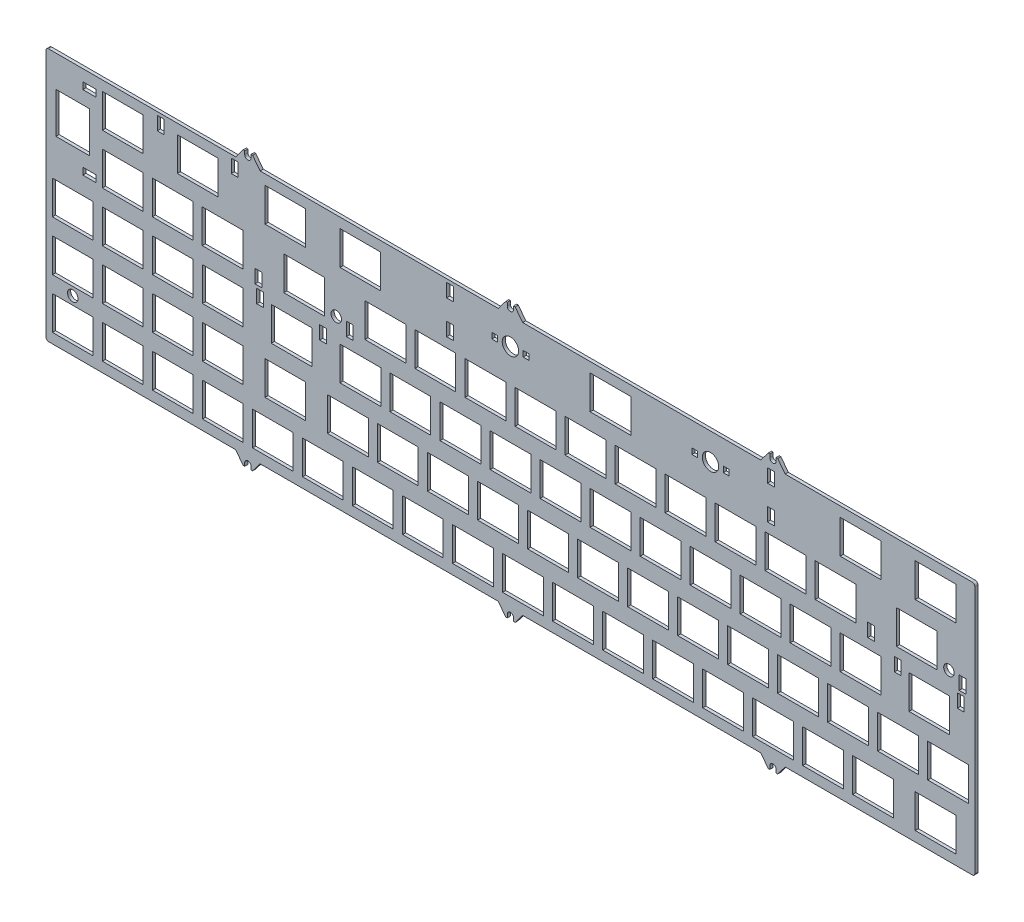
SolidWorks part; units mm, degrees
ref_plane "Front Plane" through (0, 0, 0) normal (0, 0, 1) x (1, 0, 0)
ref_plane "Top Plane" through (0, 0, 0) normal (0, 1, 0) x (1, 0, 0)
ref_plane "Right Plane" through (0, 0, 0) normal (1, 0, 0) x (0, 0, -1)
sketch "Sketch2" plane through (0, 0, 0) normal (0, 0, -1) x (1, 0, 0)
  line L0 (137.0625, 39.4) -> (121.4625, 39.4)
  line L1 (121.4625, 39.4) -> (121.4625, 26.6)
  line L2 (121.4625, 26.6) -> (137.0625, 26.6)
  line L3 (137.0625, 26.6) -> (137.0625, 39.4)
  line L4 (127.5375, 58.45) -> (111.9375, 58.45)
  line L5 (111.9375, 58.45) -> (111.9375, 45.65)
  line L6 (111.9375, 45.65) -> (127.5375, 45.65)
  line L7 (127.5375, 45.65) -> (127.5375, 58.45)
  line L8 (122.775, 77.5) -> (107.175, 77.5)
  line L9 (107.175, 77.5) -> (107.175, 64.7)
  line L10 (107.175, 64.7) -> (122.775, 64.7)
  line L11 (122.775, 64.7) -> (122.775, 77.5)
  line L12 (325.7312, 43.1) -> (325.7312, 48.2)
  line L13 (325.7312, 48.2) -> (323.1312, 48.2)
  line L14 (323.1312, 48.2) -> (323.1312, 43.1)
  line L15 (323.1312, 43.1) -> (325.7312, 43.1)
  line L16 (347.1312, 43.1) -> (347.1312, 48.2)
  line L17 (347.1312, 48.2) -> (349.7312, 48.2)
  line L18 (349.7312, 48.2) -> (349.7312, 43.1)
  line L19 (349.7312, 43.1) -> (347.1312, 43.1)
  line L20 (104.2437, 43.1) -> (104.2437, 48.2)
  line L21 (104.2437, 48.2) -> (106.8437, 48.2)
  line L22 (106.8437, 48.2) -> (106.8437, 43.1)
  line L23 (106.8437, 43.1) -> (104.2437, 43.1)
  line L24 (315.5687, 36.85) -> (315.5687, 41.95)
  line L25 (315.5687, 41.95) -> (312.9687, 41.95)
  line L26 (312.9687, 41.95) -> (312.9687, 36.85)
  line L27 (312.9687, 36.85) -> (315.5687, 36.85)
  line L28 (347.7687, 36.85) -> (347.7687, 41.95)
  line L29 (347.7687, 41.95) -> (350.3687, 41.95)
  line L30 (350.3687, 41.95) -> (350.3687, 36.85)
  line L31 (350.3687, 36.85) -> (347.7687, 36.85)
  line L32 (114.4062, 36.85) -> (114.4062, 41.95)
  line L33 (114.4062, 41.95) -> (117.0062, 41.95)
  line L34 (117.0062, 41.95) -> (117.0062, 36.85)
  line L35 (117.0062, 36.85) -> (114.4062, 36.85)
  line L36 (155.1875, 5) -> (155.1875, 10.1)
  line L37 (155.1875, 10.1) -> (152.5875, 10.1)
  line L38 (152.5875, 10.1) -> (152.5875, 5)
  line L39 (152.5875, 5) -> (155.1875, 5)
  line L40 (183.9625, 15.05) -> (183.9625, 12.85)
  line L41 (183.9625, 12.85) -> (181.7625, 12.85)
  line L42 (181.7625, 12.85) -> (181.7625, 15.05)
  line L43 (181.7625, 15.05) -> (183.9625, 15.05)
  line L44 (169.8125, 12.85) -> (169.8125, 15.05)
  line L45 (169.8125, 15.05) -> (172.0125, 15.05)
  line L46 (172.0125, 15.05) -> (172.0125, 12.85)
  line L47 (172.0125, 12.85) -> (169.8125, 12.85)
  line L48 (246.0125, 15.05) -> (246.0125, 12.85)
  line L49 (246.0125, 12.85) -> (248.2125, 12.85)
  line L50 (248.2125, 12.85) -> (248.2125, 15.05)
  line L51 (248.2125, 15.05) -> (246.0125, 15.05)
  line L52 (260.1625, 12.85) -> (260.1625, 15.05)
  line L53 (260.1625, 15.05) -> (257.9625, 15.05)
  line L54 (257.9625, 15.05) -> (257.9625, 12.85)
  line L55 (257.9625, 12.85) -> (260.1625, 12.85)
  line L56 (82.8437, 43.1) -> (82.8437, 48.2)
  line L57 (82.8437, 48.2) -> (80.2437, 48.2)
  line L58 (80.2437, 48.2) -> (80.2437, 43.1)
  line L59 (80.2437, 43.1) -> (82.8437, 43.1)
  line L60 (82.2062, 36.85) -> (82.2062, 41.95)
  line L61 (82.2062, 41.95) -> (79.6062, 41.95)
  line L62 (79.6062, 41.95) -> (79.6062, 36.85)
  line L63 (79.6062, 36.85) -> (82.2062, 36.85)
  line L64 (44.975, 5) -> (44.975, 10.1)
  line L65 (44.975, 10.1) -> (42.375, 10.1)
  line L66 (42.375, 10.1) -> (42.375, 5)
  line L67 (42.375, 5) -> (44.975, 5)
  line L68 (70.575, 5) -> (70.575, 10.1)
  line L69 (70.575, 10.1) -> (73.175, 10.1)
  line L70 (73.175, 10.1) -> (73.175, 5)
  line L71 (73.175, 5) -> (70.575, 5)
  line L72 (19.125, 10.675) -> (14.025, 10.675)
  line L73 (14.025, 10.675) -> (14.025, 8.075)
  line L74 (14.025, 8.075) -> (19.125, 8.075)
  line L75 (19.125, 8.075) -> (19.125, 10.675)
  line L76 (19.125, 36.275) -> (14.025, 36.275)
  line L77 (14.025, 36.275) -> (14.025, 38.875)
  line L78 (14.025, 38.875) -> (19.125, 38.875)
  line L79 (19.125, 38.875) -> (19.125, 36.275)
  line L80 (155.1875, 22.9) -> (155.1875, 17.8)
  line L81 (155.1875, 17.8) -> (152.5875, 17.8)
  line L82 (152.5875, 17.8) -> (152.5875, 22.9)
  line L83 (152.5875, 22.9) -> (155.1875, 22.9)
  line L84 (277.3875, 22.9) -> (277.3875, 17.8)
  line L85 (277.3875, 17.8) -> (274.7875, 17.8)
  line L86 (274.7875, 17.8) -> (274.7875, 22.9)
  line L87 (274.7875, 22.9) -> (277.3875, 22.9)
  line L88 (274.7875, 5) -> (274.7875, 10.1)
  line L89 (274.7875, 10.1) -> (277.3875, 10.1)
  line L90 (277.3875, 10.1) -> (277.3875, 5)
  line L91 (277.3875, 5) -> (274.7875, 5)
  line L92 (0, 4.75) -> (0, 99.35)
  line L93 (353.775, 4.75) -> (353.775, 99.35)
  line L94 (75.0875, 104.1) -> (72.2375, 100.35)
  line L95 (75.0875, 104.1) -> (75.6875, 104.1)
  line L96 (75.6875, 104.1) -> (75.6875, 103.6)
  line L97 (78.6875, 104.1) -> (81.5375, 100.35)
  line L98 (78.6875, 104.1) -> (78.0875, 104.1)
  line L99 (78.0875, 104.1) -> (78.0875, 103.6)
  line L100 (175.0875, 104.1) -> (172.2375, 100.35)
  line L101 (175.0875, 104.1) -> (175.6875, 104.1)
  line L102 (178.6875, 104.1) -> (181.5375, 100.35)
  line L103 (178.6875, 104.1) -> (178.0875, 104.1)
  line L104 (275.0875, 104.1) -> (272.2375, 100.35)
  line L105 (275.0875, 104.1) -> (275.6875, 104.1)
  line L106 (278.6875, 104.1) -> (281.5375, 100.35)
  line L107 (278.6875, 104.1) -> (278.0875, 104.1)
  line L108 (272.2375, 100.35) -> (181.5375, 100.35)
  line L109 (172.2375, 100.35) -> (81.5375, 100.35)
  line L110 (72.2375, 100.35) -> (1, 100.35)
  line L111 (352.775, 100.35) -> (281.5375, 100.35)
  line L112 (272.2375, 3.75) -> (181.5375, 3.75)
  line L113 (172.2375, 3.75) -> (81.5375, 3.75)
  line L114 (72.2375, 3.75) -> (1, 3.75)
  line L115 (352.775, 3.75) -> (281.5375, 3.75)
  line L116 (331.0625, 83.75) -> (346.5625, 83.75)
  line L117 (346.5625, 83.75) -> (346.5625, 96.55)
  line L118 (346.5625, 96.55) -> (331.0625, 96.55)
  line L119 (331.0625, 96.55) -> (331.0625, 83.75)
  line L120 (307.25, 83.75) -> (322.75, 83.75)
  line L121 (322.75, 83.75) -> (322.75, 96.55)
  line L122 (322.75, 96.55) -> (307.25, 96.55)
  line L123 (307.25, 96.55) -> (307.25, 83.75)
  line L124 (288.2, 83.75) -> (303.7, 83.75)
  line L125 (303.7, 83.75) -> (303.7, 96.55)
  line L126 (303.7, 96.55) -> (288.2, 96.55)
  line L127 (288.2, 96.55) -> (288.2, 83.75)
  line L128 (269.15, 83.75) -> (284.65, 83.75)
  line L129 (284.65, 83.75) -> (284.65, 96.55)
  line L130 (284.65, 96.55) -> (269.15, 96.55)
  line L131 (269.15, 96.55) -> (269.15, 83.75)
  line L132 (250.1, 83.75) -> (265.6, 83.75)
  line L133 (265.6, 83.75) -> (265.6, 96.55)
  line L134 (265.6, 96.55) -> (250.1, 96.55)
  line L135 (250.1, 96.55) -> (250.1, 83.75)
  line L136 (231.05, 83.75) -> (246.55, 83.75)
  line L137 (246.55, 83.75) -> (246.55, 96.55)
  line L138 (246.55, 96.55) -> (231.05, 96.55)
  line L139 (231.05, 96.55) -> (231.05, 83.75)
  line L140 (212, 83.75) -> (227.5, 83.75)
  line L141 (227.5, 83.75) -> (227.5, 96.55)
  line L142 (227.5, 96.55) -> (212, 96.55)
  line L143 (212, 96.55) -> (212, 83.75)
  line L144 (192.95, 83.75) -> (208.45, 83.75)
  line L145 (208.45, 83.75) -> (208.45, 96.55)
  line L146 (208.45, 96.55) -> (192.95, 96.55)
  line L147 (192.95, 96.55) -> (192.95, 83.75)
  line L148 (173.9, 83.75) -> (189.4, 83.75)
  line L149 (189.4, 83.75) -> (189.4, 96.55)
  line L150 (189.4, 96.55) -> (173.9, 96.55)
  line L151 (173.9, 96.55) -> (173.9, 83.75)
  line L152 (154.85, 83.75) -> (170.35, 83.75)
  line L153 (170.35, 83.75) -> (170.35, 96.55)
  line L154 (170.35, 96.55) -> (154.85, 96.55)
  line L155 (154.85, 96.55) -> (154.85, 83.75)
  line L156 (135.8, 83.75) -> (151.3, 83.75)
  line L157 (151.3, 83.75) -> (151.3, 96.55)
  line L158 (151.3, 96.55) -> (135.8, 96.55)
  line L159 (135.8, 96.55) -> (135.8, 83.75)
  line L160 (116.75, 83.75) -> (132.25, 83.75)
  line L161 (132.25, 83.75) -> (132.25, 96.55)
  line L162 (132.25, 96.55) -> (116.75, 96.55)
  line L163 (116.75, 96.55) -> (116.75, 83.75)
  line L164 (97.7, 83.75) -> (113.2, 83.75)
  line L165 (113.2, 83.75) -> (113.2, 96.55)
  line L166 (113.2, 96.55) -> (97.7, 96.55)
  line L167 (97.7, 96.55) -> (97.7, 83.75)
  line L168 (78.65, 83.75) -> (94.15, 83.75)
  line L169 (94.15, 83.75) -> (94.15, 96.55)
  line L170 (94.15, 96.55) -> (78.65, 96.55)
  line L171 (78.65, 96.55) -> (78.65, 83.75)
  line L172 (59.6, 77.5) -> (75.1, 77.5)
  line L173 (75.1, 64.7) -> (75.1, 77.5)
  line L174 (75.1, 96.55) -> (59.6, 96.55)
  line L175 (59.6, 77.5) -> (59.6, 64.7)
  line L176 (40.55, 77.5) -> (56.05, 77.5)
  line L177 (56.05, 64.7) -> (56.05, 77.5)
  line L178 (56.05, 96.55) -> (40.55, 96.55)
  line L179 (40.55, 77.5) -> (40.55, 64.7)
  line L180 (21.5, 77.5) -> (37, 77.5)
  line L181 (37, 64.7) -> (37, 77.5)
  line L182 (37, 96.55) -> (21.5, 96.55)
  line L183 (21.5, 77.5) -> (21.5, 64.7)
  line L184 (2.45, 77.5) -> (17.95, 77.5)
  line L185 (17.95, 64.7) -> (17.95, 77.5)
  line L186 (17.95, 96.55) -> (2.45, 96.55)
  line L187 (2.45, 77.5) -> (2.45, 64.7)
  line L188 (59.6, 64.7) -> (75.1, 64.7)
  line L189 (75.1, 83.75) -> (75.1, 96.55)
  line L190 (75.1, 83.75) -> (59.6, 83.75)
  line L191 (59.6, 96.55) -> (59.6, 83.75)
  line L192 (40.55, 64.7) -> (56.05, 64.7)
  line L193 (56.05, 83.75) -> (56.05, 96.55)
  line L194 (56.05, 83.75) -> (40.55, 83.75)
  line L195 (40.55, 96.55) -> (40.55, 83.75)
  line L196 (21.5, 64.7) -> (37, 64.7)
  line L197 (37, 83.75) -> (37, 96.55)
  line L198 (37, 83.75) -> (21.5, 83.75)
  line L199 (21.5, 96.55) -> (21.5, 83.75)
  line L200 (2.45, 64.7) -> (17.95, 64.7)
  line L201 (17.95, 83.75) -> (17.95, 96.55)
  line L202 (17.95, 83.75) -> (2.45, 83.75)
  line L203 (2.45, 96.55) -> (2.45, 83.75)
  line L204 (59.55, 45.65) -> (75.05, 45.65)
  line L205 (75.05, 45.65) -> (75.05, 58.45)
  line L206 (75.05, 58.45) -> (59.55, 58.45)
  line L207 (59.55, 58.45) -> (59.55, 45.65)
  line L208 (40.5, 45.65) -> (56, 45.65)
  line L209 (56, 45.65) -> (56, 58.45)
  line L210 (56, 58.45) -> (40.5, 58.45)
  line L211 (40.5, 58.45) -> (40.5, 45.65)
  line L212 (21.45, 45.65) -> (36.95, 45.65)
  line L213 (36.95, 45.65) -> (36.95, 58.45)
  line L214 (36.95, 58.45) -> (21.45, 58.45)
  line L215 (21.45, 58.45) -> (21.45, 45.65)
  line L216 (2.4, 45.65) -> (17.9, 45.65)
  line L217 (17.9, 45.65) -> (17.9, 58.45)
  line L218 (17.9, 58.45) -> (2.4, 58.45)
  line L219 (2.4, 58.45) -> (2.4, 45.65)
  line L220 (40.5, 26.6) -> (56, 26.6)
  line L221 (56, 26.6) -> (56, 39.4)
  line L222 (56, 39.4) -> (40.5, 39.4)
  line L223 (40.5, 39.4) -> (40.5, 26.6)
  line L224 (21.45, 26.6) -> (36.95, 26.6)
  line L225 (36.95, 26.6) -> (36.95, 39.4)
  line L226 (36.95, 39.4) -> (21.45, 39.4)
  line L227 (21.45, 39.4) -> (21.45, 26.6)
  line L232 (21.45, 7.55) -> (36.95, 7.55)
  line L233 (36.95, 7.55) -> (36.95, 20.35)
  line L234 (36.95, 20.35) -> (21.45, 20.35)
  line L235 (21.45, 20.35) -> (21.45, 7.55)
  line L236 (50.025, 7.55) -> (65.525, 7.55)
  line L237 (65.525, 7.55) -> (65.525, 20.35)
  line L238 (65.525, 20.35) -> (50.025, 20.35)
  line L239 (50.025, 20.35) -> (50.025, 7.55)
  line L240 (83.4125, 7.55) -> (98.9125, 7.55)
  line L241 (98.9125, 7.55) -> (98.9125, 20.35)
  line L242 (98.9125, 20.35) -> (83.4125, 20.35)
  line L243 (83.4125, 20.35) -> (83.4125, 7.55)
  line L244 (111.9875, 7.55) -> (127.4875, 7.55)
  line L245 (127.4875, 7.55) -> (127.4875, 20.35)
  line L246 (127.4875, 20.35) -> (111.9875, 20.35)
  line L247 (111.9875, 20.35) -> (111.9875, 7.55)
  line L248 (90.5562, 26.6) -> (106.0562, 26.6)
  line L249 (106.0562, 26.6) -> (106.0562, 39.4)
  line L250 (106.0562, 39.4) -> (90.5562, 39.4)
  line L251 (90.5562, 39.4) -> (90.5562, 26.6)
  line L252 (85.7937, 45.65) -> (101.2937, 45.65)
  line L253 (101.2937, 45.65) -> (101.2937, 58.45)
  line L254 (101.2937, 58.45) -> (85.7937, 58.45)
  line L255 (85.7937, 58.45) -> (85.7937, 45.65)
  line L256 (83.4125, 64.7) -> (98.9125, 64.7)
  line L257 (98.9125, 64.7) -> (98.9125, 77.5)
  line L258 (98.9125, 77.5) -> (83.4125, 77.5)
  line L259 (83.4125, 77.5) -> (83.4125, 64.7)
  line L260 (328.6812, 45.65) -> (344.1812, 45.65)
  line L261 (344.1812, 45.65) -> (344.1812, 58.45)
  line L262 (344.1812, 58.45) -> (328.6812, 58.45)
  line L263 (328.6812, 58.45) -> (328.6812, 45.65)
  line L264 (207.2375, 7.55) -> (222.7375, 7.55)
  line L265 (222.7375, 7.55) -> (222.7375, 20.35)
  line L266 (222.7375, 20.35) -> (207.2375, 20.35)
  line L267 (207.2375, 20.35) -> (207.2375, 7.55)
  line L268 (302.4875, 7.55) -> (317.9875, 7.55)
  line L269 (317.9875, 7.55) -> (317.9875, 20.35)
  line L270 (317.9875, 20.35) -> (302.4875, 20.35)
  line L271 (302.4875, 20.35) -> (302.4875, 7.55)
  line L272 (323.9187, 26.6) -> (339.4187, 26.6)
  line L273 (339.4187, 26.6) -> (339.4187, 39.4)
  line L274 (339.4187, 39.4) -> (323.9187, 39.4)
  line L275 (323.9187, 39.4) -> (323.9187, 26.6)
  line L276 (331.0625, 7.55) -> (346.5625, 7.55)
  line L277 (346.5625, 7.55) -> (346.5625, 20.35)
  line L278 (346.5625, 20.35) -> (331.0625, 20.35)
  line L279 (331.0625, 20.35) -> (331.0625, 7.55)
  line L280 (16.575, 15.725) -> (16.575, 31.225)
  line L281 (16.575, 31.225) -> (3.775, 31.225)
  line L282 (3.775, 31.225) -> (3.775, 15.725)
  line L283 (3.775, 15.725) -> (16.575, 15.725)
  line L284 (278.675, 64.7) -> (294.175, 64.7)
  line L285 (294.175, 64.7) -> (294.175, 77.5)
  line L286 (294.175, 77.5) -> (278.675, 77.5)
  line L287 (278.675, 77.5) -> (278.675, 64.7)
  line L288 (259.625, 64.7) -> (275.125, 64.7)
  line L289 (275.125, 64.7) -> (275.125, 77.5)
  line L290 (275.125, 77.5) -> (259.625, 77.5)
  line L291 (259.625, 77.5) -> (259.625, 64.7)
  line L292 (240.575, 64.7) -> (256.075, 64.7)
  line L293 (256.075, 64.7) -> (256.075, 77.5)
  line L294 (256.075, 77.5) -> (240.575, 77.5)
  line L295 (240.575, 77.5) -> (240.575, 64.7)
  line L296 (221.525, 64.7) -> (237.025, 64.7)
  line L297 (237.025, 64.7) -> (237.025, 77.5)
  line L298 (237.025, 77.5) -> (221.525, 77.5)
  line L299 (221.525, 77.5) -> (221.525, 64.7)
  line L300 (202.475, 64.7) -> (217.975, 64.7)
  line L301 (217.975, 64.7) -> (217.975, 77.5)
  line L302 (217.975, 77.5) -> (202.475, 77.5)
  line L303 (202.475, 77.5) -> (202.475, 64.7)
  line L304 (183.425, 64.7) -> (198.925, 64.7)
  line L305 (198.925, 64.7) -> (198.925, 77.5)
  line L306 (198.925, 77.5) -> (183.425, 77.5)
  line L307 (183.425, 77.5) -> (183.425, 64.7)
  line L308 (164.375, 64.7) -> (179.875, 64.7)
  line L309 (179.875, 64.7) -> (179.875, 77.5)
  line L310 (179.875, 77.5) -> (164.375, 77.5)
  line L311 (164.375, 77.5) -> (164.375, 64.7)
  line L312 (145.325, 64.7) -> (160.825, 64.7)
  line L313 (160.825, 64.7) -> (160.825, 77.5)
  line L314 (160.825, 77.5) -> (145.325, 77.5)
  line L315 (145.325, 77.5) -> (145.325, 64.7)
  line L316 (126.275, 64.7) -> (141.775, 64.7)
  line L317 (141.775, 64.7) -> (141.775, 77.5)
  line L318 (141.775, 77.5) -> (126.275, 77.5)
  line L319 (126.275, 77.5) -> (126.275, 64.7)
  line L320 (283.4375, 45.65) -> (298.9375, 45.65)
  line L321 (298.9375, 45.65) -> (298.9375, 58.45)
  line L322 (298.9375, 58.45) -> (283.4375, 58.45)
  line L323 (283.4375, 58.45) -> (283.4375, 45.65)
  line L324 (264.3875, 45.65) -> (279.8875, 45.65)
  line L325 (279.8875, 45.65) -> (279.8875, 58.45)
  line L326 (279.8875, 58.45) -> (264.3875, 58.45)
  line L327 (264.3875, 58.45) -> (264.3875, 45.65)
  line L328 (245.3375, 45.65) -> (260.8375, 45.65)
  line L329 (260.8375, 45.65) -> (260.8375, 58.45)
  line L330 (260.8375, 58.45) -> (245.3375, 58.45)
  line L331 (245.3375, 58.45) -> (245.3375, 45.65)
  line L332 (226.2875, 45.65) -> (241.7875, 45.65)
  line L333 (241.7875, 45.65) -> (241.7875, 58.45)
  line L334 (241.7875, 58.45) -> (226.2875, 58.45)
  line L335 (226.2875, 58.45) -> (226.2875, 45.65)
  line L336 (207.2375, 45.65) -> (222.7375, 45.65)
  line L337 (222.7375, 45.65) -> (222.7375, 58.45)
  line L338 (222.7375, 58.45) -> (207.2375, 58.45)
  line L339 (207.2375, 58.45) -> (207.2375, 45.65)
  line L340 (188.1875, 45.65) -> (203.6875, 45.65)
  line L341 (203.6875, 45.65) -> (203.6875, 58.45)
  line L342 (203.6875, 58.45) -> (188.1875, 58.45)
  line L343 (188.1875, 58.45) -> (188.1875, 45.65)
  line L344 (169.1375, 45.65) -> (184.6375, 45.65)
  line L345 (184.6375, 45.65) -> (184.6375, 58.45)
  line L346 (184.6375, 58.45) -> (169.1375, 58.45)
  line L347 (169.1375, 58.45) -> (169.1375, 45.65)
  line L348 (150.0875, 45.65) -> (165.5875, 45.65)
  line L349 (165.5875, 45.65) -> (165.5875, 58.45)
  line L350 (165.5875, 58.45) -> (150.0875, 58.45)
  line L351 (150.0875, 58.45) -> (150.0875, 45.65)
  line L352 (131.0375, 45.65) -> (146.5375, 45.65)
  line L353 (146.5375, 45.65) -> (146.5375, 58.45)
  line L354 (146.5375, 58.45) -> (131.0375, 58.45)
  line L355 (131.0375, 58.45) -> (131.0375, 45.65)
  line L356 (292.9625, 26.6) -> (308.4625, 26.6)
  line L357 (308.4625, 26.6) -> (308.4625, 39.4)
  line L358 (308.4625, 39.4) -> (292.9625, 39.4)
  line L359 (292.9625, 39.4) -> (292.9625, 26.6)
  line L360 (273.9125, 26.6) -> (289.4125, 26.6)
  line L361 (289.4125, 26.6) -> (289.4125, 39.4)
  line L362 (289.4125, 39.4) -> (273.9125, 39.4)
  line L363 (273.9125, 39.4) -> (273.9125, 26.6)
  line L364 (254.8625, 26.6) -> (270.3625, 26.6)
  line L365 (270.3625, 26.6) -> (270.3625, 39.4)
  line L366 (270.3625, 39.4) -> (254.8625, 39.4)
  line L367 (254.8625, 39.4) -> (254.8625, 26.6)
  line L368 (235.8125, 26.6) -> (251.3125, 26.6)
  line L369 (251.3125, 26.6) -> (251.3125, 39.4)
  line L370 (251.3125, 39.4) -> (235.8125, 39.4)
  line L371 (235.8125, 39.4) -> (235.8125, 26.6)
  line L372 (216.7625, 26.6) -> (232.2625, 26.6)
  line L373 (232.2625, 26.6) -> (232.2625, 39.4)
  line L374 (232.2625, 39.4) -> (216.7625, 39.4)
  line L375 (216.7625, 39.4) -> (216.7625, 26.6)
  line L376 (197.7125, 26.6) -> (213.2125, 26.6)
  line L377 (213.2125, 26.6) -> (213.2125, 39.4)
  line L378 (213.2125, 39.4) -> (197.7125, 39.4)
  line L379 (197.7125, 39.4) -> (197.7125, 26.6)
  line L380 (178.6625, 26.6) -> (194.1625, 26.6)
  line L381 (194.1625, 26.6) -> (194.1625, 39.4)
  line L382 (194.1625, 39.4) -> (178.6625, 39.4)
  line L383 (178.6625, 39.4) -> (178.6625, 26.6)
  line L384 (159.6125, 26.6) -> (175.1125, 26.6)
  line L385 (175.1125, 26.6) -> (175.1125, 39.4)
  line L386 (175.1125, 39.4) -> (159.6125, 39.4)
  line L387 (159.6125, 39.4) -> (159.6125, 26.6)
  line L388 (140.5625, 26.6) -> (156.0625, 26.6)
  line L389 (156.0625, 26.6) -> (156.0625, 39.4)
  line L390 (156.0625, 39.4) -> (140.5625, 39.4)
  line L391 (140.5625, 39.4) -> (140.5625, 26.6)
  line L392 (335.825, 64.7) -> (351.325, 64.7)
  line L393 (351.325, 64.7) -> (351.325, 77.5)
  line L394 (351.325, 77.5) -> (335.825, 77.5)
  line L395 (335.825, 77.5) -> (335.825, 64.7)
  line L396 (316.775, 64.7) -> (332.275, 64.7)
  line L397 (332.275, 64.7) -> (332.275, 77.5)
  line L398 (332.275, 77.5) -> (316.775, 77.5)
  line L399 (316.775, 77.5) -> (316.775, 64.7)
  line L400 (297.725, 64.7) -> (313.225, 64.7)
  line L401 (313.225, 64.7) -> (313.225, 77.5)
  line L402 (313.225, 77.5) -> (297.725, 77.5)
  line L403 (297.725, 77.5) -> (297.725, 64.7)
  line L404 (302.4875, 45.65) -> (317.9875, 45.65)
  line L405 (317.9875, 45.65) -> (317.9875, 58.45)
  line L406 (317.9875, 58.45) -> (302.4875, 58.45)
  line L407 (302.4875, 58.45) -> (302.4875, 45.65)
  line L408 (278.0875, 102.85) -> (278.0875, 104.1)
  line L409 (275.6875, 102.85) -> (275.6875, 104.1)
  line L410 (178.0875, 102.85) -> (178.0875, 104.1)
  line L411 (175.6875, 102.85) -> (175.6875, 104.1)
  line L412 (78.0875, 102.85) -> (78.0875, 103.6)
  line L413 (75.6875, 102.85) -> (75.6875, 103.6)
  line L414 (75.0875, 0) -> (72.2375, 3.75)
  line L415 (75.0875, 0) -> (75.6875, 0)
  line L416 (75.6875, 0) -> (75.6875, 0.5)
  line L417 (78.6875, 0) -> (81.5375, 3.75)
  line L418 (78.6875, 0) -> (78.0875, 0)
  line L419 (78.0875, 0) -> (78.0875, 0.5)
  line L420 (175.0875, 0) -> (172.2375, 3.75)
  line L421 (175.0875, 0) -> (175.6875, 0)
  line L422 (178.6875, 0) -> (181.5375, 3.75)
  line L423 (178.6875, 0) -> (178.0875, 0)
  line L424 (275.0875, 0) -> (272.2375, 3.75)
  line L425 (275.0875, 0) -> (275.6875, 0)
  line L426 (278.6875, 0) -> (281.5375, 3.75)
  line L427 (278.6875, 0) -> (278.0875, 0)
  line L428 (278.0875, 1.25) -> (278.0875, 0)
  line L429 (275.6875, 1.25) -> (275.6875, 0)
  line L430 (178.0875, 1.25) -> (178.0875, 0)
  line L431 (175.6875, 1.25) -> (175.6875, 0)
  line L432 (78.0875, 1.25) -> (78.0875, 0.5)
  line L433 (75.6875, 1.25) -> (75.6875, 0.5)
  line L439 (59.5, 26.6) -> (75, 26.6)
  line L440 (75, 39.4) -> (59.5, 39.4)
  line L441 (75, 26.6) -> (75, 39.4)
  line L442 (59.5, 39.4) -> (59.5, 26.6)
  circle A0 centre (176.8875, 13.95) radius 3.125
  circle A1 centre (253.0875, 13.95) radius 3.125
  arc A2 (0, 4.75) -> (1, 3.75) centre (1, 4.75) ccw
  arc A3 (1, 100.35) -> (0, 99.35) centre (1, 99.35) ccw
  arc A4 (75.6875, 102.85) -> (78.0875, 102.85) centre (76.8875, 102.85) ccw
  arc A5 (175.6875, 102.85) -> (178.0875, 102.85) centre (176.8875, 102.85) ccw
  arc A6 (275.6875, 102.85) -> (278.0875, 102.85) centre (276.8875, 102.85) ccw
  arc A7 (352.775, 3.75) -> (353.775, 4.75) centre (352.775, 4.75) ccw
  arc A8 (353.775, 99.35) -> (352.775, 100.35) centre (352.775, 99.35) ccw
  circle A9 centre (343.9187, 37.25) radius 2
  circle A10 centre (110.5562, 37.25) radius 2
  circle A11 centre (10.2, 80.625) radius 2
  arc A12 (78.0875, 1.25) -> (75.6875, 1.25) centre (76.8875, 1.25) ccw
  arc A13 (178.0875, 1.25) -> (175.6875, 1.25) centre (176.8875, 1.25) ccw
  arc A14 (278.0875, 1.25) -> (275.6875, 1.25) centre (276.8875, 1.25) ccw
extrude "Boss-Extrude1" add sketch "Sketch2" against normal blind 1.2 contours L428 A14 L429 L425 L424 L112 L422 L423 L430 A13 L431 L421 L420 L113 L417 L418 L419 L432 A12 L433 L416 L415 L414 L114 A2 L92 A3 L110 L94 L95 L96 L413 A4 L412 L99 L98 L97 L109 L100 L101 L411 A5 L410 L103 L102 L108 L104 L105 L409 A6 L408
